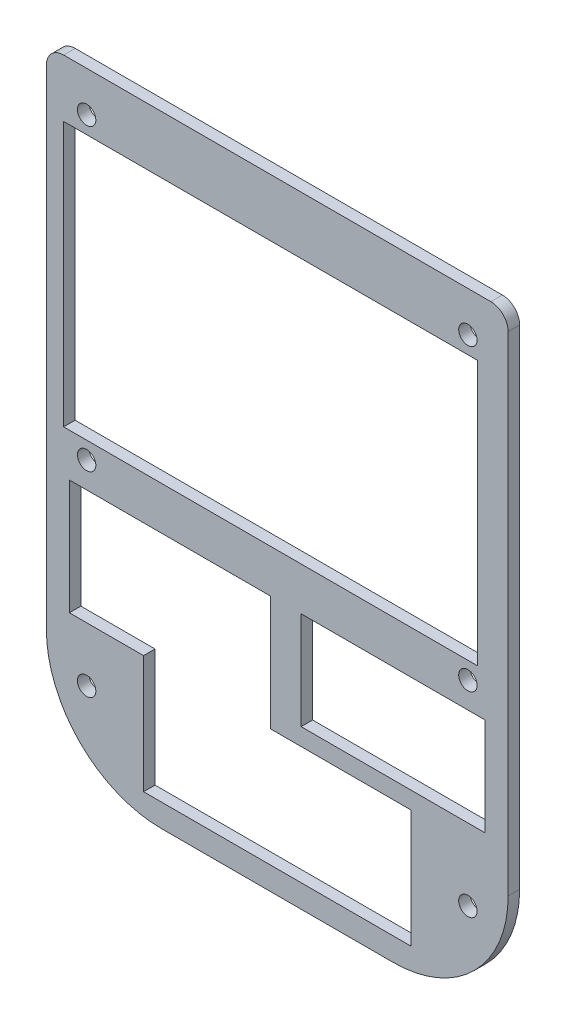
SolidWorks part; units mm, degrees
material "Acrylic (Medium-high impact)"
ref_plane "Front Plane" through (0, 0, 0) normal (0, 0, 1) x (1, 0, 0)
ref_plane "Top Plane" through (0, 0, 0) normal (0, 1, 0) x (1, 0, 0)
ref_plane "Right Plane" through (0, 0, 0) normal (1, 0, 0) x (0, 0, -1)
sketch "Sketch1" plane through (0, 0, 0) normal (0, 0, 1) x (1, 0, 0)
  line L1 (0, 0) -> (80.3, 0)
  line L2 (0, 0) -> (0, 66)
  line L3 (0, 66) -> (80.3, 66)
  line L4 (80.3, 0) -> (80.3, 66)
  dimension "D1" = 80.3
  dimension "D2" = 66
extrude "Boss-Extrude1" add sketch "Sketch1" along normal blind 2
hole_wizard "Ø3.2 (3.2) Diameter Hole1" positions "Sketch3" profile "Sketch2" hole size "Ø3.2" standard "ANSI Metric" end condition through all
sketch "Sketch3" plane through (0, 0, 2) normal (0, 0, 1) x (1, 0, 0)
  line L0 (0, 33) -> (80.3, 33) construction
  line L1 (0, 66) -> (0, 0) construction
  line L2 (80.3, 0) -> (80.3, 66) construction
  line L4 (7, 7) -> (7, 59) construction
  line L6 (7, 59) -> (73.3, 59) construction
  line L7 (73.3, 59) -> (73.3, 7) construction
  line L8 (73.3, 7) -> (7, 7) construction
  line L10 (40.15, 66) -> (40.15, 0) construction
  line L11 (80.3, 66) -> (0, 66) construction
  line L12 (0, 0) -> (80.3, 0) construction
  point P0 (7, 59)
  point P2 (73.3, 59)
  point P4 (73.3, 7)
  point P6 (7, 7)
  dimension "D1" = 66.3
  dimension "D2" = 52
  dimension "D3" = 26
  dimension "D4" = 33.15
sketch "Sketch2" plane through (7, 59, 2) normal (1, 0, 0) x (0, -1, 0)
  line L0 (0, 0) -> (0, 2)
  line L1 (0, 2) -> (1.6, 2)
  line L2 (1.6, 2) -> (1.6, 0)
  line L5 (1.6, 0) -> (0, 0)
  line L11 (0, -6.35) -> (0, 107.95) construction
  dimension "Thru Hole Dia." = 3.2
  dimension "Thru Hole Depth" = 2
fillet "Fillet1" radius 3 2 edges at (80.3, 66, 1) (0, 66, 1)
sketch "Sketch4" plane through (0, 0, 0) normal (0, -1, 0) x (1, 0, 0)
  line L4 (0, 0) -> (80.3, 0)
  line L5 (80.3, 0) -> (80.3, 2)
  line L6 (80.3, 2) -> (0, 2)
  line L7 (0, 2) -> (0, 0)
  line L8 (0, 0) -> (80.3, 0)
  line L9 (80.3, 0) -> (80.3, 2)
  line L10 (80.3, 2) -> (0, 2)
  line L11 (0, 2) -> (0, 0)
  dimension "D1" = 0
extrude "Boss-Extrude2" add sketch "Sketch4" along normal blind 42
fillet "Fillet2" radius 20 2 edges at (0, -42, 1) (80.3, -42, 1)
hole_wizard "Ø3.2 (3.2) Diameter Hole2" positions "Sketch6" profile "Sketch5" hole size "Ø3.2" standard "ANSI Metric"
sketch "Sketch6" plane through (0, 0, 2) normal (0, 0, 1) x (1, 0, 0)
  line L0 (7, -27) -> (73.3, -27) construction
  line L2 (40.15, -42) -> (40.15, 66) construction
  line L3 (60.3, -42) -> (20, -42) construction
  line L4 (77.3, 66) -> (3, 66) construction
  line L5 (40.15, -27) -> (40.15, -42) construction
  line L7 (0, 63) -> (0, -22) construction
  point P0 (7, -27)
  point P2 (73.3, -27)
  dimension "D1" = 15
  dimension "D2" = 7
sketch "Sketch5" plane through (7, -27, 2) normal (1, 0, 0) x (0, -1, 0)
  line L0 (0, 0) -> (0, 60.9614)
  line L1 (0, 60.9614) -> (1.6, 60)
  line L2 (1.6, 60) -> (1.6, 0)
  line L5 (1.6, 0) -> (0, 0)
  line L10 (0, 60.9614) -> (-1.6, 60) construction
  line L11 (0, -6.35) -> (0, 107.95) construction
  dimension "Hole Dia." = 3.2
  dimension "Hole Depth" = 60
  dimension "Drill Angle" = 118
sketch "Sketch7" plane through (0, 0, 2) normal (0, 0, 1) x (1, 0, 0)
  line L0 (3, 33) -> (75, 33) construction
  line L1 (3, 56) -> (75, 56)
  line L2 (3, 56) -> (3, 10)
  line L3 (3, 10) -> (75, 10)
  line L4 (75, 56) -> (75, 10)
  line L5 (7, 59) -> (7, 7) construction
  line L6 (7, 33) -> (80.3, 33) construction
  line L7 (80.3, -22) -> (80.3, 63) construction
  circle A0 centre (7, 59) radius 1.6 construction
  dimension "D1" = 72
  dimension "D2" = 46
  dimension "D3" = 4
extrude "Cut-Extrude1" cut sketch "Sketch7" against normal through all
sketch "Sketch10" plane through (0, 0, 2) normal (0, 0, 1) x (1, 0, 0)
  line L0 (76.3, -6) -> (44.3, -6) construction
  line L1 (4, 2.5) -> (39, 2.5)
  line L2 (4, 2.5) -> (4, -17.5)
  line L3 (4, -17.5) -> (39, -17.5)
  line L4 (39, 2.5) -> (39, -17.5)
  line L5 (44.3, 2.5) -> (76.3, 2.5)
  line L6 (44.3, 2.5) -> (44.3, -14.5)
  line L7 (44.3, -14.5) -> (76.3, -14.5)
  line L8 (76.3, 2.5) -> (76.3, -14.5)
  line L9 (16.9, -17.5) -> (63.4, -17.5)
  line L10 (16.9, -17.5) -> (16.9, -38)
  line L11 (16.9, -38) -> (63.4, -38)
  line L12 (63.4, -17.5) -> (63.4, -38)
  line L13 (39, -7.5) -> (4, -7.5) construction
  line L14 (40.15, -17.5) -> (40.15, -38) construction
  line L15 (40.15, -42) -> (40.15, 10) construction
  line L16 (60.3, -42) -> (20, -42) construction
  line L17 (3, 10) -> (75, 10) construction
  line L18 (0, 63) -> (0, -22) construction
  line L19 (80.3, -22) -> (80.3, 63) construction
  dimension "D1" = 32
  dimension "D2" = 17
  dimension "D3" = 35
  dimension "D4" = 20
  dimension "D5" = 20.5
  dimension "D6" = 46.5
  dimension "D7" = 7.5
  dimension "D8" = 4
  dimension "D9" = 4
extrude "Cut-Extrude3" cut sketch "Sketch10" against normal through all contours L4 L1 L2 L3 | L12 L9 L3 L10 L11 | L8 L5 L6 L7
